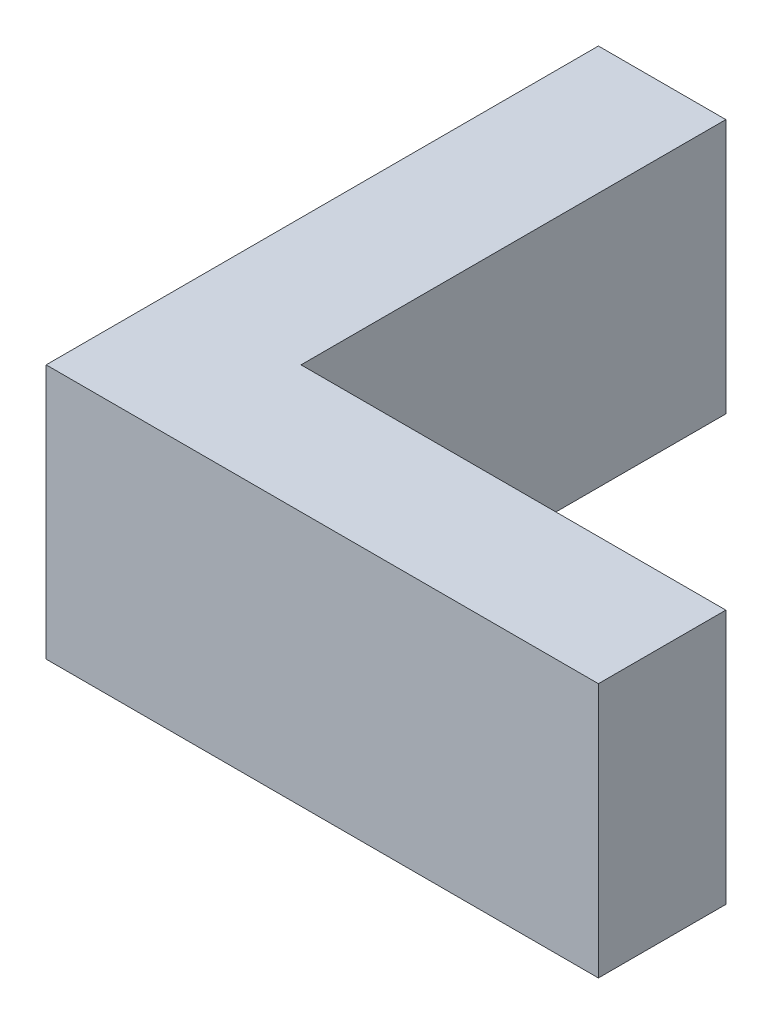
SolidWorks part; units mm, degrees
ref_plane "Alzado" through (0, 0, 0) normal (0, 0, 1) x (1, 0, 0)
ref_plane "Planta" through (0, 0, 0) normal (0, 1, 0) x (1, 0, 0)
ref_plane "Vista lateral" through (0, 0, 0) normal (1, 0, 0) x (0, 0, -1)
sketch "Croquis1" plane through (0, 0, 0) normal (0, 1, 0) x (1, 0, 0)
  line L0 (0, 0) -> (0, 20)
  line L1 (0, 20) -> (-6, 20)
  line L2 (-6, 20) -> (-6, -6)
  line L3 (-6, -6) -> (20, -6)
  line L4 (20, -6) -> (20, 0)
  line L5 (20, 0) -> (0, 0)
  dimension "D1" = 20
  dimension "D2" = 6
extrude "Saliente-Extruir1" add sketch "Croquis1" along normal blind 12
